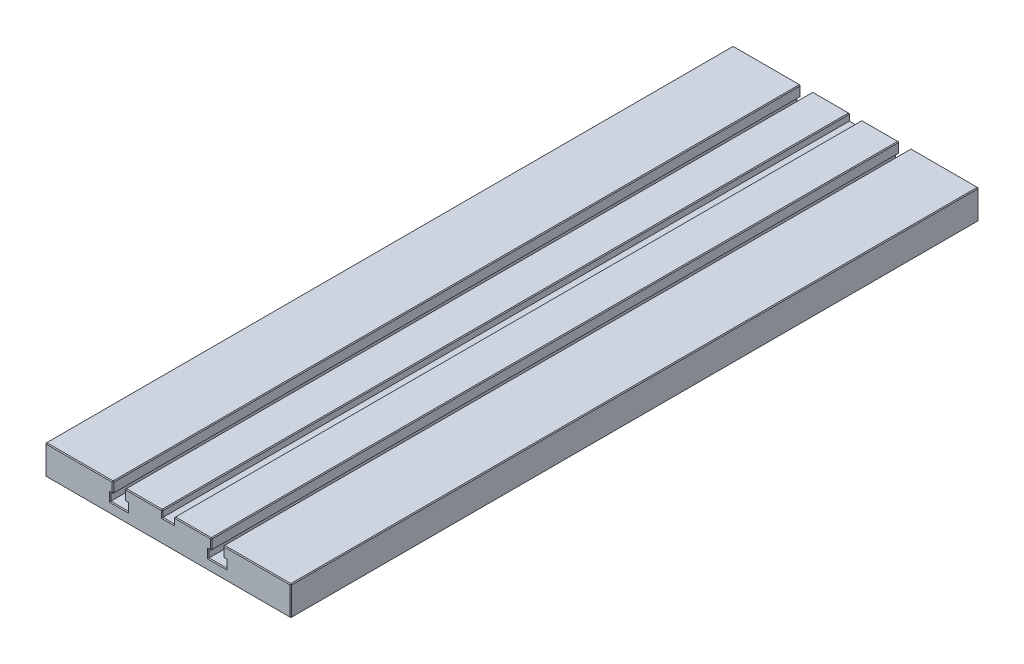
SolidWorks part; units mm, degrees
ref_plane "Alzado" through (0, 0, 0) normal (0, 0, 1) x (1, 0, 0)
ref_plane "Planta" through (0, 0, 0) normal (0, 1, 0) x (1, 0, 0)
ref_plane "Vista lateral" through (0, 0, 0) normal (1, 0, 0) x (0, 0, -1)
sketch "Croquis1" plane through (0, 0, 0) normal (0, 0, 1) x (1, 0, 0)
  line L1 (125, -15) -> (-125, -15)
  line L2 (125, -15) -> (125, 15)
  line L3 (125, 15) -> (-125, 15)
  line L4 (-125, -15) -> (-125, 15)
  line L5 (125, -15) -> (-125, 15) construction
  line L6 (125, 15) -> (-125, -15) construction
  point P0 (0, 0)
  dimension "D1" = 250
  dimension "D2" = 30
extrude "Saliente-Extruir1" add sketch "Croquis1" along normal blind 700
sketch "Croquis3" plane through (0, 0, 700) normal (0, 0, 1) x (1, 0, 0)
  line L0 (0, 34.0666) -> (0, -41.9975) construction
  line L1 (-50, 48.4864) -> (-50, -50.2889) construction
  line L2 (50, 43.8) -> (50, -50.2889) construction
  line L3 (-56, 15) -> (-56, 4.83)
  line L4 (125, 15) -> (-125, 15) construction
  line L5 (-56.8, 4.03) -> (-59, 4.03)
  line L6 (-59, 4.03) -> (-59, -3.97)
  line L7 (-59, -3.97) -> (-41, -3.97)
  line L8 (-41, -3.97) -> (-41, 4.03)
  line L9 (-41, 4.03) -> (-43.2, 4.03)
  line L10 (-44, 4.83) -> (-44, 15)
  line L11 (-56, 15) -> (-44, 15)
  line L12 (-56, 4.83) -> (-56.8, 4.03)
  line L13 (-43.2, 4.03) -> (-44, 4.83)
  line L14 (41, -3.97) -> (41, 4.03)
  line L15 (59, -3.97) -> (41, -3.97)
  line L16 (59, 4.03) -> (59, -3.97)
  line L17 (56.8, 4.03) -> (59, 4.03)
  line L18 (56, 4.83) -> (56.8, 4.03)
  line L19 (43.2, 4.03) -> (44, 4.83)
  line L20 (41, 4.03) -> (43.2, 4.03)
  line L21 (44, 4.83) -> (44, 15)
  line L22 (56, 15) -> (44, 15)
  line L23 (56, 15) -> (56, 4.83)
  line L25 (6, 8.2) -> (-6, 8.2)
  line L26 (6, 8.2) -> (6, 21.8)
  line L27 (6, 21.8) -> (-6, 21.8)
  line L28 (-6, 8.2) -> (-6, 21.8)
  line L29 (6, 8.2) -> (-6, 21.8) construction
  line L30 (6, 21.8) -> (-6, 8.2) construction
  point P8 (-56, 4.03)
  point P16 (-44, 4.03)
  point P31 (0, 15)
  dimension "D1" = 50
  dimension "D2" = 50
  dimension "D3" = 12
  dimension "D4" = 18
  dimension "D5" = 10.97
  dimension "D6" = 8
  dimension "D7" = 12
  dimension "D8" = 6.8
extrude "Cortar-Extruir1" cut sketch "Croquis3" against normal blind 794.2
chamfer "Chaflán1" distance 0.8 angle 45 66 edges at (44, 15, 350) (6, 15, 350) (0, 8.2, 700) (6, 11.6, 700) (25, 15, 700) (44, 9.915, 700) (43.6, 4.43, 700) (42.1, 4.03, 700) (41, 0.03, 700) (50, -3.97, 700) (59, 0.03, 700) (57.9, 4.03, 700) (56.4, 4.43, 700) (56, 9.915, 700) (90.5, 15, 700) (125, 0, 700) (-90.5, 15, 700) (-56, 9.915, 700) (-56.4, 4.43, 700) (-57.9, 4.03, 700) (-59, 0.03, 700) (-50, -3.97, 700) (-41, 0.03, 700) (-42.1, 4.03, 700) (-43.6, 4.43, 700) (-44, 9.915, 700) (-25, 15, 700) (-6, 11.6, 700) (0, -15, 700) (125, -15, 350) (-44, 9.915, 0) (-43.6, 4.43, 0) (-42.1, 4.03, 0) (-41, 0.03, 0) (-50, -3.97, 0) (-59, 0.03, 0) (-57.9, 4.03, 0) (-56.4, 4.43, 0) (-56, 9.915, 0) (-56, 15, 350) (-90.5, 15, 0) (-125, 15, 350) (-125, 0, 700) (-125, -15, 350) (-125, 0, 0) (0, -15, 0) (125, 0, 0) (-44, 15, 350) (-25, 15, 0) (-6, 15, 350) (-6, 11.6, 0) (0, 8.2, 0) (6, 11.6, 0) (25, 15, 0) (44, 9.915, 0) (43.6, 4.43, 0) (42.1, 4.03, 0) (41, 0.03, 0) (50, -3.97, 0) (59, 0.03, 0) (57.9, 4.03, 0) (56.4, 4.43, 0) (56, 9.915, 0) (56, 15, 350) (90.5, 15, 0) (125, 15, 350)
